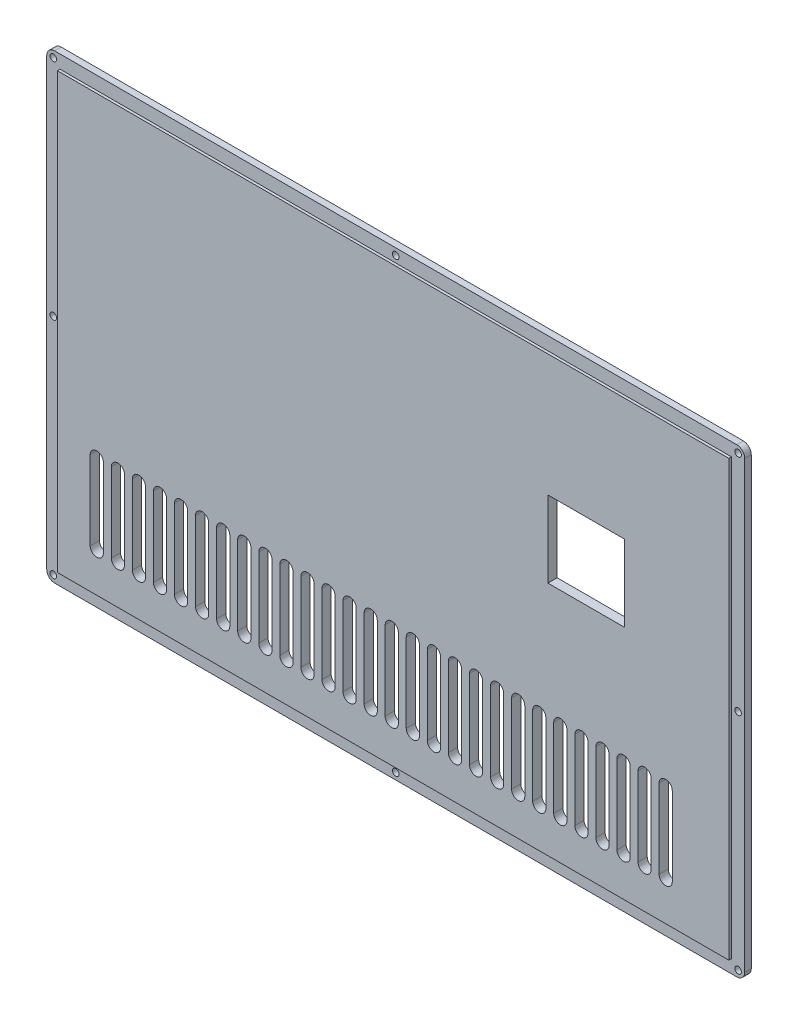
SolidWorks part; units mm, degrees
ref_plane "Front Plane" through (0, 0, 0) normal (0, 0, 1) x (1, 0, 0)
ref_plane "Top Plane" through (0, 0, 0) normal (0, 1, 0) x (1, 0, 0)
ref_plane "Right Plane" through (0, 0, 0) normal (1, 0, 0) x (0, 0, -1)
sketch "Sketch1" plane through (0, 0, 0) normal (0, 0, 1) x (1, 0, 0)
  line L1 (-132.5, 87.5) -> (132.5, 87.5)
  line L2 (-132.5, 87.5) -> (-132.5, -87.5)
  line L3 (-132.5, -87.5) -> (132.5, -87.5)
  line L4 (132.5, 87.5) -> (132.5, -87.5)
  point P4 (-132.5, 0)
  point P6 (0, 87.5)
  dimension "D1" = 265
  dimension "D2" = 175
extrude "Boss-Extrude1" add sketch "Sketch1" along normal blind 2.5
sketch "Sketch2" plane through (0, 0, 2.5) normal (0, 0, 1) x (1, 0, 0)
  line L0 (132.5, 87.5) -> (-132.5, 87.5) construction
  line L1 (-127.5, 82.5) -> (127.5, 82.5)
  line L2 (-127.5, 82.5) -> (-127.5, -82.5)
  line L3 (-127.5, -82.5) -> (127.5, -82.5)
  line L4 (127.5, 82.5) -> (127.5, -82.5)
  line L5 (-132.5, 87.5) -> (-132.5, -87.5) construction
  point P4 (-127.5, 0)
  point P6 (0, 82.5)
  dimension "D1" = 5
  dimension "D2" = 5
extrude "Boss-Extrude2" add sketch "Sketch2" along normal blind 1
sketch "Sketch3" plane through (0, 0, 0) normal (0, 0, -1) x (-1, 0, 0)
  line L0 (132.5, -87.5) -> (-132.5, -87.5) construction
  line L1 (132.5, 87.5) -> (132.5, -87.5) construction
  line L2 (110, -67.5) -> (110, -37.5)
  line L3 (115, -67.5) -> (115, -37.5)
  arc A0 (110, -67.5) -> (115, -67.5) centre (112.5, -67.5) ccw
  arc A1 (115, -37.5) -> (110, -37.5) centre (112.5, -37.5) ccw
  point P11 (112.5, -35)
  point P15 (112.5, -70)
  dimension "D1" = 5
  dimension "D2" = 20
  dimension "D3" = 20
  dimension "D4" = 30
extrude "Cut-Extrude1" cut sketch "Sketch3" against normal through all
pattern_linear "LPattern1" count 28 spacing 8 along (1, 0, 0) of "Cut-Extrude1"
mirror "Mirror2" [suppressed] about plane through (0, 0, 0) normal (0, 1, 0)
fillet "Fillet3" radius 3 4 edges at (132.5, -87.5, 1.25) (132.5, 87.5, 1.25) (-132.5, 87.5, 1.25) (-132.5, -87.5, 1.25)
sketch "Sketch5" plane through (0, 0, 0) normal (0, 0, -1) x (-1, 0, 0)
  line L1 (-58.78, 7.14) -> (-87.78, 7.14)
  line L2 (-58.78, 7.14) -> (-58.78, 36.14)
  line L3 (-58.78, 36.14) -> (-87.78, 36.14)
  line L4 (-87.78, 7.14) -> (-87.78, 36.14)
  line L5 (-132.5, -84.5) -> (-132.5, 84.5) construction
  point P4 (-58.78, 21.64)
  point P5 (-73.28, 7.14)
  dimension "D1" = 29
  dimension "D2" = 29
  dimension "D3" = 21.64
  dimension "D4" = 59.22
extrude "Cut-Extrude3" cut sketch "Sketch5" against normal through all
sketch "Sketch7" plane through (0, 0, 0) normal (0, 0, -1) x (-1, 0, 0)
  line L0 (-129.5, 87.5) -> (129.5, 87.5) construction
  line L1 (130, 85) -> (-130, 85) construction
  line L2 (130, 85) -> (130, -85) construction
  line L3 (130, -85) -> (-130, -85) construction
  line L4 (-130, 85) -> (-130, -85) construction
  line L5 (129.5, -87.5) -> (-129.5, -87.5) construction
  line L6 (132.5, 84.5) -> (132.5, -84.5) construction
  line L7 (-132.5, -84.5) -> (-132.5, 84.5) construction
  circle A0 centre (130, -85) radius 1.25
  circle A1 centre (130, 0) radius 1.25
  circle A2 centre (130, 85) radius 1.25
  circle A3 centre (0, 85) radius 1.25
  circle A4 centre (-130, 85) radius 1.25
  circle A5 centre (-130, 0) radius 1.25
  circle A6 centre (-130, -85) radius 1.25
  circle A7 centre (0, -85) radius 1.25
  dimension "D5" = 2.5
  dimension "D1" = 2.5
  dimension "D2" = 2.5
  dimension "D3" = 2.5
  dimension "D4" = 2.5
extrude "Cut-Extrude4" cut sketch "Sketch7" against normal through all
sketch "Sketch8" plane through (0, 0, 0) normal (0, 0, -1) x (-1, 0, 0)
  line L0 (69.0973, 92.1728) -> (202.4306, 92.1728) construction
  line L1 (85.3423, 47.1146) -> (-9.836, 47.1146)
  line L2 (-33.6608, 23.2899) -> (-33.6608, 20.6474)
  line L3 (-9.836, -3.1774) -> (85.3423, -3.1774)
  line L4 (109.167, 20.6474) -> (109.167, 23.2899)
  line L5 (9.765, 10.2781) -> (10.9597, 11.2255)
  line L6 (24.4102, 24.4248) -> (22.062, 24.4248)
  line L7 (32.0726, 29.8453) -> (30.8984, 28.8759)
  line L8 (22.062, 26.0112) -> (24.4102, 26.0112)
  line L9 (24.4102, 21.2516) -> (22.062, 21.2516)
  line L10 (34.4002, 31.8285) -> (33.2466, 30.837)
  line L11 (22.062, 22.8382) -> (24.3277, 22.8382)
  line L12 (12.0719, 12.2611) -> (13.2254, 13.2529)
  line L13 (22.062, 19.665) -> (24.3277, 19.665)
  line L14 (14.3995, 14.2446) -> (15.5736, 15.2139)
  line L15 (24.4102, 18.0785) -> (22.062, 18.0785)
  line L16 (36.7071, 33.8117) -> (35.5125, 32.8641)
  line L17 (62.0839, 16.6943) -> (63.2168, 15.7467)
  line L18 (63.2373, 28.7028) -> (62.0632, 27.7966)
  line L19 (64.4114, 14.8404) -> (65.5237, 13.8723)
  line L20 (65.5649, 30.5566) -> (64.4114, 29.6298)
  line L21 (66.6773, 12.9454) -> (67.8514, 12.0389)
  line L22 (67.8719, 32.4105) -> (66.6773, 31.5247)
  line L23 (93.1662, 16.6943) -> (94.299, 15.7467)
  line L24 (94.3196, 28.7028) -> (93.1455, 27.7966)
  line L25 (95.4936, 14.8404) -> (96.606, 13.8723)
  line L26 (96.6472, 30.5566) -> (95.4936, 29.6298)
  line L27 (97.7595, 12.9454) -> (98.9336, 12.0389)
  line L28 (98.9542, 32.4105) -> (97.7595, 31.5247)
  line L29 (132.5, 0) -> (-55.3342, 0) construction
  line L30 (132.5, 84.5) -> (132.5, -84.5) construction
  spline S0 degree 3 poles (2.0716, 26.8386) (1.4466, 28.3012) (0.6021, 29.5644) (-0.4619, 30.6288) knots 15 15 15 15 16 16 16 16
  spline S1 degree 3 poles (2.0716, 17.6314) (2.6963, 19.0939) (3.0088, 20.6285) (3.0088, 22.2352) (3.0088, 23.8418) (2.6963, 25.3762) (2.0716, 26.8386) knots 13 13 13 13 14 14 14 15 15 15 15
  spline S2 degree 3 poles (-0.4619, 13.8415) (0.6021, 14.9055) (1.4466, 16.169) (2.0716, 17.6314) knots 12 12 12 12 13 13 13 13
  spline S3 degree 3 poles (-4.252, 11.3078) (-2.7895, 11.9325) (-1.5263, 12.777) (-0.4619, 13.8415) knots 11 11 11 11 12 12 12 12
  spline S4 degree 3 poles (-13.4592, 11.3078) (-11.9968, 10.6829) (-10.4622, 10.3707) (-8.8556, 10.3707) (-7.249, 10.3707) (-5.7145, 10.6829) (-4.252, 11.3078) knots 9 9 9 9 10 10 10 11 11 11 11
  spline S5 degree 3 poles (-17.2493, 13.8415) (-16.1853, 12.777) (-14.9217, 11.9325) (-13.4592, 11.3078) knots 8 8 8 8 9 9 9 9
  spline S6 degree 3 poles (-19.7829, 17.6314) (-19.1581, 16.169) (-18.3137, 14.9055) (-17.2493, 13.8415) knots 7 7 7 7 8 8 8 8
  spline S7 degree 3 poles (-19.7829, 26.8386) (-20.4079, 25.3762) (-20.7201, 23.8418) (-20.7201, 22.2352) (-20.7201, 20.6285) (-20.4079, 19.0939) (-19.7829, 17.6314) knots 5 5 5 5 6 6 6 7 7 7 7
  spline S8 degree 3 poles (-17.2493, 30.6288) (-18.3137, 29.5644) (-19.1581, 28.3012) (-19.7829, 26.8386) knots 4 4 4 4 5 5 5 5
  spline S9 degree 3 poles (-13.4592, 33.1623) (-14.9217, 32.5372) (-16.1853, 31.6928) (-17.2493, 30.6288) knots 3 3 3 3 4 4 4 4
  spline S10 degree 3 poles (-4.252, 33.1623) (-5.7145, 33.7871) (-7.249, 34.0996) (-8.8556, 34.0996) (-10.4622, 34.0996) (-11.9968, 33.7871) (-13.4592, 33.1623) knots 1 1 1 1 2 2 2 3 3 3 3
  spline S11 degree 3 poles (-0.4619, 30.6288) (-1.5263, 31.6928) (-2.7895, 32.5372) (-4.252, 33.1623) knots 0 0 0 0 1 1 1 1
  spline S12 degree 3 poles (0.1354, 27.4464) (1.0623, 25.8531) (1.5257, 24.1164) (1.5257, 22.2352) (1.5257, 20.3536) (1.0623, 18.6165) (0.1354, 17.0238) knots 10 10 10 10 11 11 11 12 12 12 12
  spline S13 degree 3 poles (-3.6443, 31.226) (-2.0515, 30.2993) (-0.7915, 29.0393) (0.1354, 27.4464) knots 9 9 9 9 10 10 10 10
  spline S14 degree 3 poles (-14.0669, 31.226) (-12.4741, 32.153) (-10.7372, 32.6165) (-8.8556, 32.6165) (-6.9744, 32.6165) (-5.2375, 32.153) (-3.6443, 31.226) knots 7 7 7 7 8 8 8 9 9 9 9
  spline S15 degree 3 poles (-17.8467, 27.4464) (-16.9197, 29.0393) (-15.6601, 30.2993) (-14.0669, 31.226) knots 6 6 6 6 7 7 7 7
  spline S16 degree 3 poles (-17.8467, 17.0238) (-18.7735, 18.6165) (-19.237, 20.3536) (-19.237, 22.2352) (-19.237, 24.1164) (-18.7735, 25.8531) (-17.8467, 27.4464) knots 4 4 4 4 5 5 5 6 6 6 6
  spline S17 degree 3 poles (-14.0669, 13.244) (-15.6601, 14.171) (-16.9197, 15.4307) (-17.8467, 17.0238) knots 3 3 3 3 4 4 4 4
  spline S18 degree 3 poles (-3.6443, 13.244) (-5.2375, 12.3172) (-6.9744, 11.8536) (-8.8556, 11.8536) (-10.7372, 11.8536) (-12.4741, 12.3172) (-14.0669, 13.244) knots 1 1 1 1 2 2 2 3 3 3 3
  spline S19 degree 3 poles (0.1354, 17.0238) (-0.7915, 15.4307) (-2.0515, 14.171) (-3.6443, 13.244) knots 0 0 0 0 1 1 1 1
  spline S20 degree 3 poles (-2.563, 28.5175) (-4.3003, 30.2612) (-6.3977, 31.1334) (-8.8556, 31.1334) knots 7 7 7 7 8 8 8 8
  spline S21 degree 3 poles (-2.563, 15.9527) (-0.8259, 17.6964) (0.0427, 19.7906) (0.0427, 22.2352) (0.0427, 24.6791) (-0.8259, 26.7734) (-2.563, 28.5175) knots 5 5 5 5 6 6 6 7 7 7 7
  spline S22 degree 3 poles (-15.1483, 15.9527) (-13.4113, 14.2086) (-11.3138, 13.3367) (-8.8556, 13.3367) (-6.3977, 13.3367) (-4.3003, 14.2086) (-2.563, 15.9527) knots 3 3 3 3 4 4 4 5 5 5 5
  spline S23 degree 3 poles (-15.1483, 28.5175) (-16.8857, 26.7734) (-17.754, 24.6791) (-17.754, 22.2352) (-17.754, 19.7906) (-16.8857, 17.6964) (-15.1483, 15.9527) knots 1 1 1 1 2 2 2 3 3 3 3
  spline S24 degree 3 poles (-8.8556, 31.1334) (-11.3138, 31.1334) (-13.4113, 30.2612) (-15.1483, 28.5175) knots 0 0 0 0 1 1 1 1
  spline S25 degree 3 poles (4.8009, 27.9922) (4.0181, 29.8254) (2.964, 31.4045) (1.639, 32.7298) knots 15 15 15 15 16 16 16 16
  spline S26 degree 3 poles (4.8009, 16.478) (5.5836, 18.3112) (5.9749, 20.2301) (5.9749, 22.2352) (5.9749, 24.2399) (5.5836, 26.159) (4.8009, 27.9922) knots 13 13 13 13 14 14 14 15 15 15 15
  spline S27 degree 3 poles (1.639, 11.7404) (2.964, 13.0655) (4.0181, 14.6446) (4.8009, 16.478) knots 12 12 12 12 13 13 13 13
  spline S28 degree 3 poles (-3.0985, 8.5786) (-1.2652, 9.3612) (0.3137, 10.4151) (1.639, 11.7404) knots 11 11 11 11 12 12 12 12
  spline S29 degree 3 poles (-14.6128, 8.5786) (-12.7795, 7.796) (-10.8607, 7.4045) (-8.8556, 7.4045) (-6.8509, 7.4045) (-4.9317, 7.796) (-3.0985, 8.5786) knots 9 9 9 9 10 10 10 11 11 11 11
  spline S30 degree 3 poles (-19.3503, 11.7404) (-18.0253, 10.4151) (-16.446, 9.3612) (-14.6128, 8.5786) knots 8 8 8 8 9 9 9 9
  spline S31 degree 3 poles (-22.5121, 16.478) (-21.7294, 14.6446) (-20.6757, 13.0655) (-19.3503, 11.7404) knots 7 7 7 7 8 8 8 8
  spline S32 degree 3 poles (-22.5121, 27.9922) (-23.2948, 26.159) (-23.6862, 24.2399) (-23.6862, 22.2352) (-23.6862, 20.2301) (-23.2948, 18.3112) (-22.5121, 16.478) knots 5 5 5 5 6 6 6 7 7 7 7
  spline S33 degree 3 poles (-19.3503, 32.7298) (-20.6757, 31.4045) (-21.7294, 29.8254) (-22.5121, 27.9922) knots 4 4 4 4 5 5 5 5
  spline S34 degree 3 poles (-14.6128, 35.8915) (-16.446, 35.1088) (-18.0253, 34.0547) (-19.3503, 32.7298) knots 3 3 3 3 4 4 4 4
  spline S35 degree 3 poles (-3.0985, 35.8915) (-4.9317, 36.6743) (-6.8509, 37.0656) (-8.8556, 37.0656) (-10.8607, 37.0656) (-12.7795, 36.6743) (-14.6128, 35.8915) knots 1 1 1 1 2 2 2 3 3 3 3
  spline S36 degree 3 poles (1.639, 32.7298) (0.3137, 34.0547) (-1.2652, 35.1088) (-3.0985, 35.8915) knots 0 0 0 0 1 1 1 1
  spline S37 degree 3 poles (3.4311, 27.4257) (4.1381, 25.778) (4.4919, 24.0478) (4.4919, 22.2352) (4.4919, 20.4225) (4.1381, 18.6922) (3.4311, 17.0443) knots 14 14 14 14 15 15 15 16 16 16 16
  spline S38 degree 3 poles (0.5885, 31.6792) (1.7762, 30.4914) (2.7237, 29.0737) (3.4311, 27.4257) knots 13 13 13 13 14 14 14 14
  spline S39 degree 3 poles (-3.6649, 34.5217) (-2.0171, 33.8143) (-0.5994, 32.8669) (0.5885, 31.6792) knots 12 12 12 12 13 13 13 13
  spline S40 degree 3 poles (-14.0463, 34.5217) (-12.3985, 35.2288) (-10.6682, 35.5825) (-8.8556, 35.5825) (-7.043, 35.5825) (-5.3128, 35.2288) (-3.6649, 34.5217) knots 10 10 10 10 11 11 11 12 12 12 12
  spline S41 degree 3 poles (-18.2998, 31.6792) (-17.1122, 32.8669) (-15.6942, 33.8143) (-14.0463, 34.5217) knots 9 9 9 9 10 10 10 10
  spline S42 degree 3 poles (-21.1423, 27.4257) (-20.4352, 29.0737) (-19.4878, 30.4914) (-18.2998, 31.6792) knots 8 8 8 8 9 9 9 9
  spline S43 degree 3 poles (-21.1423, 17.0443) (-21.8498, 18.6922) (-22.2031, 20.4225) (-22.2031, 22.2352) (-22.2031, 24.0478) (-21.8498, 25.778) (-21.1423, 27.4257) knots 6 6 6 6 7 7 7 8 8 8 8
  spline S44 degree 3 poles (-18.2998, 12.7909) (-19.4878, 13.9786) (-20.4352, 15.3966) (-21.1423, 17.0443) knots 5 5 5 5 6 6 6 6
  spline S45 degree 3 poles (-14.0463, 9.9483) (-15.6942, 10.6554) (-17.1122, 11.6029) (-18.2998, 12.7909) knots 4 4 4 4 5 5 5 5
  spline S46 degree 3 poles (-3.6649, 9.9483) (-5.3128, 9.241) (-7.043, 8.8876) (-8.8556, 8.8876) (-10.6682, 8.8876) (-12.3985, 9.241) (-14.0463, 9.9483) knots 2 2 2 2 3 3 3 4 4 4 4
  spline S47 degree 3 poles (0.5885, 12.7909) (-0.5994, 11.6029) (-2.0171, 10.6554) (-3.6649, 9.9483) knots 1 1 1 1 2 2 2 2
  spline S48 degree 3 poles (3.4311, 17.0443) (2.7237, 15.3966) (1.7762, 13.9786) (0.5885, 12.7909) knots 0 0 0 0 1 1 1 1
  spline S49 degree 3 poles (-9.836, 47.1146) (-22.9941, 47.1146) (-33.6608, 36.4479) (-33.6608, 23.2899) knots 1 1 1 1 2 2 2 2
  spline S50 degree 3 poles (-33.6608, 20.6474) (-33.6608, 7.4893) (-22.9941, -3.1774) (-9.836, -3.1774) knots 3 3 3 3 4 4 4 4
  spline S51 degree 3 poles (85.3423, -3.1774) (98.5003, -3.1774) (109.167, 7.4893) (109.167, 20.6474) knots 5 5 5 5 6 6 6 6
  spline S52 degree 3 poles (109.167, 23.2899) (109.167, 36.4479) (98.5003, 47.1146) (85.3423, 47.1146) knots 7 7 7 7 8 8 8 8
  spline S53 degree 3 poles (6.1603, 28.569) (7.0254, 26.5571) (7.458, 24.4459) (7.458, 22.2352) (7.458, 20.0241) (7.0254, 17.9127) (6.1603, 15.9012) knots 14 14 14 14 15 15 15 16 16 16 16
  spline S54 degree 3 poles (2.6792, 33.7701) (4.1346, 32.3143) (5.2952, 30.5805) (6.1603, 28.569) knots 13 13 13 13 14 14 14 14
  spline S55 degree 3 poles (-2.5217, 37.2509) (-0.5102, 36.3859) (1.2235, 35.2253) (2.6792, 33.7701) knots 12 12 12 12 13 13 13 13
  spline S56 degree 3 poles (-15.1895, 37.2509) (-13.178, 38.116) (-11.0667, 38.5486) (-8.8556, 38.5486) (-6.6449, 38.5486) (-4.5336, 38.116) (-2.5217, 37.2509) knots 10 10 10 10 11 11 11 12 12 12 12
  spline S57 degree 3 poles (-20.3905, 33.7701) (-18.9351, 35.2253) (-17.2014, 36.3859) (-15.1895, 37.2509) knots 9 9 9 9 10 10 10 10
  spline S58 degree 3 poles (-23.8715, 28.569) (-23.0065, 30.5805) (-21.8462, 32.3143) (-20.3905, 33.7701) knots 8 8 8 8 9 9 9 9
  spline S59 degree 3 poles (-23.8715, 15.9012) (-24.7366, 17.9127) (-25.1693, 20.0241) (-25.1693, 22.2352) (-25.1693, 24.4459) (-24.7366, 26.5571) (-23.8715, 28.569) knots 6 6 6 6 7 7 7 8 8 8 8
  spline S60 degree 3 poles (-20.3905, 10.7003) (-21.8462, 12.1555) (-23.0065, 13.8893) (-23.8715, 15.9012) knots 5 5 5 5 6 6 6 6
  spline S61 degree 3 poles (-15.1895, 7.2191) (-17.2014, 8.0841) (-18.9351, 9.2445) (-20.3905, 10.7003) knots 4 4 4 4 5 5 5 5
  spline S62 degree 3 poles (-2.5217, 7.2191) (-4.5336, 6.354) (-6.6449, 5.9214) (-8.8556, 5.9214) (-11.0667, 5.9214) (-13.178, 6.354) (-15.1895, 7.2191) knots 2 2 2 2 3 3 3 4 4 4 4
  spline S63 degree 3 poles (2.6792, 10.7003) (1.2235, 9.2445) (-0.5102, 8.0841) (-2.5217, 7.2191) knots 1 1 1 1 2 2 2 2
  spline S64 degree 3 poles (6.1603, 15.9012) (5.2952, 13.8893) (4.1346, 12.1555) (2.6792, 10.7003) knots 0 0 0 0 1 1 1 1
  spline S65 degree 3 poles (35.4713, 11.7545) (34.8808, 10.5058) (34.0325, 9.4078) (32.9274, 8.4604) knots 0 0 0 0 1 1 1 1
  spline S66 degree 3 poles (32.9274, 8.4604) (31.8218, 7.5126) (30.4109, 6.7636) (28.6945, 6.2127) knots 1 1 1 1 2 2 2 2
  spline S67 degree 3 poles (28.6945, 6.2127) (26.9778, 5.6617) (25.0692, 5.3862) (22.9683, 5.3862) knots 2 2 2 2 3 3 3 3
  spline S68 degree 3 poles (22.9683, 5.3862) (20.3179, 5.3862) (17.8394, 5.816) (15.5324, 6.6754) knots 3 3 3 3 4 4 4 4
  spline S69 degree 3 poles (15.5324, 6.6754) (13.2254, 7.5347) (11.3027, 8.7357) (9.765, 10.2781) knots 4 4 4 4 5 5 5 5
  spline S70 degree 3 poles (10.9597, 11.2255) (12.3603, 9.8738) (14.1112, 8.8272) (16.2121, 8.0855) knots 6 6 6 6 7 7 7 7
  spline S71 degree 3 poles (16.2121, 8.0855) (18.3132, 7.3436) (20.565, 6.9728) (22.9683, 6.9728) knots 7 7 7 7 8 8 8 8
  spline S72 degree 3 poles (22.9683, 6.9728) (26.6759, 6.9728) (29.5871, 7.8102) (31.7018, 9.4848) knots 8 8 8 8 9 9 9 9
  spline S73 degree 3 poles (31.7018, 9.4848) (33.8163, 11.1596) (34.874, 13.2529) (34.874, 15.7649) knots 9 9 9 9 10 10 10 10
  spline S74 degree 3 poles (34.874, 15.7649) (34.874, 18.4236) (33.9677, 20.5317) (32.155, 22.0888) knots 10 10 10 10 11 11 11 11
  spline S75 degree 3 poles (32.155, 22.0888) (30.3424, 23.646) (27.7605, 24.4248) (24.4102, 24.4248) knots 11 11 11 11 12 12 12 12
  spline S76 degree 3 poles (22.062, 24.4248) (18.0521, 24.4248) (16.0474, 25.7247) (16.0474, 28.325) knots 13 13 13 13 14 14 14 14
  spline S77 degree 3 poles (16.0474, 28.325) (16.0474, 29.5) (16.6685, 30.4658) (17.9115, 31.2226) knots 14 14 14 14 15 15 15 15
  spline S78 degree 3 poles (17.9115, 31.2226) (19.1542, 31.9791) (21.0182, 32.3573) (23.5038, 32.3573) knots 15 15 15 15 16 16 16 16
  spline S79 degree 3 poles (23.5038, 32.3573) (25.2476, 32.3573) (26.8681, 32.1404) (28.365, 31.7073) knots 16 16 16 16 17 17 17 17
  spline S80 degree 3 poles (28.365, 31.7073) (29.8615, 31.2738) (31.0973, 30.6531) (32.0726, 29.8453) knots 17 17 17 17 18 18 18 18
  spline S81 degree 3 poles (30.8984, 28.8759) (29.1819, 30.139) (26.7171, 30.7707) (23.5038, 30.7707) knots 19 19 19 19 20 20 20 20
  spline S82 degree 3 poles (23.5038, 30.7707) (21.444, 30.7707) (19.9333, 30.5429) (18.9723, 30.0876) knots 20 20 20 20 21 21 21 21
  spline S83 degree 3 poles (18.9723, 30.0876) (18.0109, 29.6323) (17.5304, 29.0445) (17.5304, 28.325) knots 21 21 21 21 22 22 22 22
  spline S84 degree 3 poles (17.5304, 28.325) (17.5304, 27.4876) (17.8667, 26.8925) (18.5397, 26.54) knots 22 22 22 22 23 23 23 23
  spline S85 degree 3 poles (18.5397, 26.54) (19.2124, 26.1874) (20.3865, 26.0112) (22.062, 26.0112) knots 23 23 23 23 24 24 24 24
  spline S86 degree 3 poles (24.4102, 26.0112) (28.2275, 26.0112) (31.173, 25.0818) (33.2466, 23.2239) knots 25 25 25 25 26 26 26 26
  spline S87 degree 3 poles (33.2466, 23.2239) (35.3199, 21.3652) (36.3569, 18.879) (36.3569, 15.7649) knots 26 26 26 26 27 27 27 27
  spline S88 degree 3 poles (36.3569, 15.7649) (36.3569, 14.3399) (36.0615, 13.0029) (35.4713, 11.7545) knots 27 27 27 27 28 28 28 28
  spline S89 degree 3 poles (30.0231, 19.8303) (28.7666, 20.7777) (26.8955, 21.2516) (24.4102, 21.2516) knots 0 0 0 0 1 1 1 1
  spline S90 degree 3 poles (22.062, 21.2516) (19.1783, 21.2516) (16.9605, 21.8796) (15.4088, 23.1356) knots 2 2 2 2 3 3 3 3
  spline S91 degree 3 poles (15.4088, 23.1356) (13.8569, 24.3917) (13.0813, 26.1214) (13.0813, 28.325) knots 3 3 3 3 4 4 4 4
  spline S92 degree 3 poles (13.0813, 28.325) (13.0813, 30.3813) (13.9944, 32.0963) (15.8207, 33.47) knots 4 4 4 4 5 5 5 5
  spline S93 degree 3 poles (15.8207, 33.47) (17.647, 34.8436) (20.2082, 35.5304) (23.5038, 35.5304) knots 5 5 5 5 6 6 6 6
  spline S94 degree 3 poles (23.5038, 35.5304) (25.7008, 35.5304) (27.7503, 35.2071) (29.6523, 34.5607) knots 6 6 6 6 7 7 7 7
  spline S95 degree 3 poles (29.6523, 34.5607) (31.5541, 33.9143) (33.1367, 33.0035) (34.4002, 31.8285) knots 7 7 7 7 8 8 8 8
  spline S96 degree 3 poles (33.2466, 30.837) (32.1206, 31.8209) (30.706, 32.5849) (29.0035, 33.1286) knots 9 9 9 9 10 10 10 10
  spline S97 degree 3 poles (29.0035, 33.1286) (27.3007, 33.6717) (25.4673, 33.9439) (23.5038, 33.9439) knots 10 10 10 10 11 11 11 11
  spline S98 degree 3 poles (23.5038, 33.9439) (20.6063, 33.9439) (18.392, 33.4149) (16.8609, 32.3573) knots 11 11 11 11 12 12 12 12
  spline S99 degree 3 poles (16.8609, 32.3573) (15.3296, 31.2997) (14.5643, 29.9555) (14.5643, 28.325) knots 12 12 12 12 13 13 13 13
  spline S100 degree 3 poles (14.5643, 28.325) (14.5643, 26.5621) (15.1926, 25.2069) (16.449, 24.2595) knots 13 13 13 13 14 14 14 14
  spline S101 degree 3 poles (16.449, 24.2595) (17.7055, 23.3119) (19.5763, 22.8382) (22.062, 22.8382) knots 14 14 14 14 15 15 15 15
  spline S102 degree 3 poles (24.3277, 22.8382) (27.2526, 22.8382) (29.4944, 22.2102) (31.053, 20.9542) knots 16 16 16 16 17 17 17 17
  spline S103 degree 3 poles (31.053, 20.9542) (32.6114, 19.6982) (33.3909, 17.9683) (33.3909, 15.7649) knots 17 17 17 17 18 18 18 18
  spline S104 degree 3 poles (33.3909, 15.7649) (33.3909, 13.7081) (32.4774, 11.9931) (30.6514, 10.6197) knots 18 18 18 18 19 19 19 19
  spline S105 degree 3 poles (30.6514, 10.6197) (28.8248, 9.2458) (26.264, 8.5594) (22.9683, 8.5594) knots 19 19 19 19 20 20 20 20
  spline S106 degree 3 poles (22.9683, 8.5594) (20.7711, 8.5594) (18.7215, 8.8823) (16.8198, 9.5289) knots 20 20 20 20 21 21 21 21
  spline S107 degree 3 poles (16.8198, 9.5289) (14.9177, 10.1752) (13.3352, 11.0859) (12.0719, 12.2611) knots 21 21 21 21 22 22 22 22
  spline S108 degree 3 poles (13.2254, 13.2529) (14.3512, 12.2686) (15.7658, 11.5045) (17.4686, 10.9612) knots 23 23 23 23 24 24 24 24
  spline S109 degree 3 poles (17.4686, 10.9612) (19.1712, 10.4175) (21.0044, 10.146) (22.9683, 10.146) knots 24 24 24 24 25 25 25 25
  spline S110 degree 3 poles (22.9683, 10.146) (25.8656, 10.146) (28.0798, 10.6748) (29.6111, 11.7325) knots 25 25 25 25 26 26 26 26
  spline S111 degree 3 poles (29.6111, 11.7325) (31.1422, 12.7901) (31.9078, 14.1344) (31.9078, 15.7649) knots 26 26 26 26 27 27 27 27
  spline S112 degree 3 poles (31.9078, 15.7649) (31.9078, 17.5277) (31.2795, 18.8829) (30.0231, 19.8303) knots 27 27 27 27 28 28 28 28
  spline S113 degree 3 poles (35.5125, 32.8641) (34.1117, 34.2156) (32.361, 35.262) (30.2599, 36.0041) knots 0 0 0 0 1 1 1 1
  spline S114 degree 3 poles (30.2599, 36.0041) (28.159, 36.7459) (25.9067, 37.117) (23.5038, 37.117) knots 1 1 1 1 2 2 2 2
  spline S115 degree 3 poles (23.5038, 37.117) (19.7962, 37.117) (16.8848, 36.2796) (14.7703, 34.605) knots 2 2 2 2 3 3 3 3
  spline S116 degree 3 poles (14.7703, 34.605) (12.6555, 32.9302) (11.5982, 30.837) (11.5982, 28.325) knots 3 3 3 3 4 4 4 4
  spline S117 degree 3 poles (11.5982, 28.325) (11.5982, 25.6659) (12.5045, 23.5578) (14.3171, 22.0008) knots 4 4 4 4 5 5 5 5
  spline S118 degree 3 poles (14.3171, 22.0008) (16.1297, 20.4434) (18.7113, 19.665) (22.062, 19.665) knots 5 5 5 5 6 6 6 6
  spline S119 degree 3 poles (24.3277, 19.665) (28.3923, 19.665) (30.4247, 18.3651) (30.4247, 15.7649) knots 7 7 7 7 8 8 8 8
  spline S120 degree 3 poles (30.4247, 15.7649) (30.4247, 14.5895) (29.8034, 13.6236) (28.5607, 12.8672) knots 8 8 8 8 9 9 9 9
  spline S121 degree 3 poles (28.5607, 12.8672) (27.3177, 12.1104) (25.4536, 11.7325) (22.9683, 11.7325) knots 9 9 9 9 10 10 10 10
  spline S122 degree 3 poles (22.9683, 11.7325) (21.2242, 11.7325) (19.6037, 11.949) (18.1072, 12.3825) knots 10 10 10 10 11 11 11 11
  spline S123 degree 3 poles (18.1072, 12.3825) (16.6102, 12.8156) (15.3744, 13.4364) (14.3995, 14.2446) knots 11 11 11 11 12 12 12 12
  spline S124 degree 3 poles (15.5736, 15.2139) (17.29, 13.9505) (19.755, 13.3189) (22.9683, 13.3189) knots 13 13 13 13 14 14 14 14
  spline S125 degree 3 poles (22.9683, 13.3189) (25.0282, 13.3189) (26.5384, 13.5466) (27.4999, 14.002) knots 14 14 14 14 15 15 15 15
  spline S126 degree 3 poles (27.4999, 14.002) (28.4608, 14.4571) (28.9418, 15.0449) (28.9418, 15.7649) knots 15 15 15 15 16 16 16 16
  spline S127 degree 3 poles (28.9418, 15.7649) (28.9418, 16.6021) (28.6051, 17.1971) (27.9324, 17.5497) knots 16 16 16 16 17 17 17 17
  spline S128 degree 3 poles (27.9324, 17.5497) (27.2595, 17.9024) (26.0853, 18.0785) (24.4102, 18.0785) knots 17 17 17 17 18 18 18 18
  spline S129 degree 3 poles (22.062, 18.0785) (18.2443, 18.0785) (15.2988, 19.0075) (13.2254, 20.866) knots 19 19 19 19 20 20 20 20
  spline S130 degree 3 poles (13.2254, 20.866) (11.1518, 22.7243) (10.1152, 25.2103) (10.1152, 28.325) knots 20 20 20 20 21 21 21 21
  spline S131 degree 3 poles (10.1152, 28.325) (10.1152, 29.7496) (10.4102, 31.0864) (11.0009, 32.3353) knots 21 21 21 21 22 22 22 22
  spline S132 degree 3 poles (11.0009, 32.3353) (11.5911, 33.5837) (12.4391, 34.6821) (13.5447, 35.6295) knots 22 22 22 22 23 23 23 23
  spline S133 degree 3 poles (13.5447, 35.6295) (14.65, 36.5771) (16.0609, 37.3262) (17.7776, 37.8772) knots 23 23 23 23 24 24 24 24
  spline S134 degree 3 poles (17.7776, 37.8772) (19.494, 38.4281) (21.4028, 38.7034) (23.5038, 38.7034) knots 24 24 24 24 25 25 25 25
  spline S135 degree 3 poles (23.5038, 38.7034) (26.1539, 38.7034) (28.6328, 38.2736) (30.9397, 37.4145) knots 25 25 25 25 26 26 26 26
  spline S136 degree 3 poles (30.9397, 37.4145) (33.2466, 36.5549) (35.1691, 35.354) (36.7071, 33.8117) knots 26 26 26 26 27 27 27 27
  spline S137 degree 3 poles (48.8291, 15.9527) (50.566, 14.2086) (52.6635, 13.3367) (55.1217, 13.3367) knots 0 0 0 0 1 1 1 1
  spline S138 degree 3 poles (55.1217, 13.3367) (56.4948, 13.3367) (57.7924, 13.6355) (59.0147, 14.2326) knots 1 1 1 1 2 2 2 2
  spline S139 degree 3 poles (59.0147, 14.2326) (60.2368, 14.8301) (61.2599, 15.6505) (62.0839, 16.6943) knots 2 2 2 2 3 3 3 3
  spline S140 degree 3 poles (63.2168, 15.7467) (62.2555, 14.5382) (61.0675, 13.5871) (59.6532, 12.8939) knots 4 4 4 4 5 5 5 5
  spline S141 degree 3 poles (59.6532, 12.8939) (58.2387, 12.2004) (56.7283, 11.8536) (55.1217, 11.8536) knots 5 5 5 5 6 6 6 6
  spline S142 degree 3 poles (55.1217, 11.8536) (53.2403, 11.8536) (51.5032, 12.3172) (49.9105, 13.244) knots 6 6 6 6 7 7 7 7
  spline S143 degree 3 poles (49.9105, 13.244) (48.3174, 14.171) (47.0577, 15.4307) (46.1307, 17.0238) knots 7 7 7 7 8 8 8 8
  spline S144 degree 3 poles (46.1307, 17.0238) (45.2038, 18.6165) (44.7403, 20.3536) (44.7403, 22.2352) knots 8 8 8 8 9 9 9 9
  spline S145 degree 3 poles (44.7403, 22.2352) (44.7403, 24.1164) (45.2038, 25.8531) (46.1307, 27.4464) knots 9 9 9 9 10 10 10 10
  spline S146 degree 3 poles (46.1307, 27.4464) (47.0577, 29.0393) (48.3174, 30.2993) (49.9105, 31.226) knots 10 10 10 10 11 11 11 11
  spline S147 degree 3 poles (49.9105, 31.226) (51.5032, 32.153) (53.2403, 32.6165) (55.1217, 32.6165) knots 11 11 11 11 12 12 12 12
  spline S148 degree 3 poles (55.1217, 32.6165) (56.7283, 32.6165) (58.2424, 32.2696) (59.6635, 31.5762) knots 12 12 12 12 13 13 13 13
  spline S149 degree 3 poles (59.6635, 31.5762) (61.0848, 30.8827) (62.276, 29.9249) (63.2373, 28.7028) knots 13 13 13 13 14 14 14 14
  spline S150 degree 3 poles (62.0632, 27.7966) (61.2393, 28.8399) (60.2198, 29.6571) (59.0044, 30.2478) knots 15 15 15 15 16 16 16 16
  spline S151 degree 3 poles (59.0044, 30.2478) (57.7891, 30.838) (56.4948, 31.1334) (55.1217, 31.1334) knots 16 16 16 16 17 17 17 17
  spline S152 degree 3 poles (55.1217, 31.1334) (52.6635, 31.1334) (50.566, 30.2612) (48.8291, 28.5175) knots 17 17 17 17 18 18 18 18
  spline S153 degree 3 poles (48.8291, 28.5175) (47.0918, 26.7734) (46.2234, 24.6791) (46.2234, 22.2352) knots 18 18 18 18 19 19 19 19
  spline S154 degree 3 poles (46.2234, 22.2352) (46.2234, 19.7906) (47.0918, 17.6964) (48.8291, 15.9527) knots 19 19 19 19 20 20 20 20
  spline S155 degree 3 poles (60.3125, 32.9048) (58.692, 33.7012) (56.9618, 34.0996) (55.1217, 34.0996) knots 0 0 0 0 1 1 1 1
  spline S156 degree 3 poles (55.1217, 34.0996) (53.515, 34.0996) (51.9806, 33.7871) (50.518, 33.1623) knots 1 1 1 1 2 2 2 2
  spline S157 degree 3 poles (50.518, 33.1623) (49.0556, 32.5372) (47.7921, 31.6928) (46.728, 30.6288) knots 2 2 2 2 3 3 3 3
  spline S158 degree 3 poles (46.728, 30.6288) (45.6637, 29.5644) (44.8191, 28.3012) (44.1945, 26.8386) knots 3 3 3 3 4 4 4 4
  spline S159 degree 3 poles (44.1945, 26.8386) (43.5695, 25.3762) (43.2572, 23.8418) (43.2572, 22.2352) knots 4 4 4 4 5 5 5 5
  spline S160 degree 3 poles (43.2572, 22.2352) (43.2572, 20.6285) (43.5695, 19.0939) (44.1945, 17.6314) knots 5 5 5 5 6 6 6 6
  spline S161 degree 3 poles (44.1945, 17.6314) (44.8191, 16.169) (45.6637, 14.9055) (46.728, 13.8415) knots 6 6 6 6 7 7 7 7
  spline S162 degree 3 poles (46.728, 13.8415) (47.7921, 12.777) (49.0556, 11.9325) (50.518, 11.3078) knots 7 7 7 7 8 8 8 8
  spline S163 degree 3 poles (50.518, 11.3078) (51.9806, 10.6829) (53.515, 10.3707) (55.1217, 10.3707) knots 8 8 8 8 9 9 9 9
  spline S164 degree 3 poles (55.1217, 10.3707) (56.9618, 10.3707) (58.692, 10.7688) (60.3125, 11.5653) knots 9 9 9 9 10 10 10 10
  spline S165 degree 3 poles (60.3125, 11.5653) (61.9325, 12.3615) (63.2991, 13.4531) (64.4114, 14.8404) knots 10 10 10 10 11 11 11 11
  spline S166 degree 3 poles (65.5237, 13.8723) (64.2739, 12.3205) (62.743, 11.1018) (60.9303, 10.2162) knots 12 12 12 12 13 13 13 13
  spline S167 degree 3 poles (60.9303, 10.2162) (59.1177, 9.3304) (57.1815, 8.8876) (55.1217, 8.8876) knots 13 13 13 13 14 14 14 14
  spline S168 degree 3 poles (55.1217, 8.8876) (53.309, 8.8876) (51.5789, 9.241) (49.931, 9.9483) knots 14 14 14 14 15 15 15 15
  spline S169 degree 3 poles (49.931, 9.9483) (48.2831, 10.6554) (46.8651, 11.6029) (45.6776, 12.7909) knots 15 15 15 15 16 16 16 16
  spline S170 degree 3 poles (45.6776, 12.7909) (44.4896, 13.9786) (43.542, 15.3966) (42.8351, 17.0443) knots 16 16 16 16 17 17 17 17
  spline S171 degree 3 poles (42.8351, 17.0443) (42.1277, 18.6922) (41.7743, 20.4225) (41.7743, 22.2352) knots 17 17 17 17 18 18 18 18
  spline S172 degree 3 poles (41.7743, 22.2352) (41.7743, 24.0478) (42.1277, 25.778) (42.8351, 27.4257) knots 18 18 18 18 19 19 19 19
  spline S173 degree 3 poles (42.8351, 27.4257) (43.542, 29.0737) (44.4896, 30.4914) (45.6776, 31.6792) knots 19 19 19 19 20 20 20 20
  spline S174 degree 3 poles (45.6776, 31.6792) (46.8651, 32.8669) (48.2831, 33.8143) (49.931, 34.5217) knots 20 20 20 20 21 21 21 21
  spline S175 degree 3 poles (49.931, 34.5217) (51.5789, 35.2288) (53.309, 35.5825) (55.1217, 35.5825) knots 21 21 21 21 22 22 22 22
  spline S176 degree 3 poles (55.1217, 35.5825) (57.1951, 35.5825) (59.1415, 35.1362) (60.9613, 34.2437) knots 22 22 22 22 23 23 23 23
  spline S177 degree 3 poles (60.9613, 34.2437) (62.7806, 33.3509) (64.3152, 32.122) (65.5649, 30.5566) knots 23 23 23 23 24 24 24 24
  spline S178 degree 3 poles (64.4114, 29.6298) (63.2991, 31.0165) (61.9325, 32.1083) (60.3125, 32.9048) knots 25 25 25 25 26 26 26 26
  spline S179 degree 3 poles (61.5791, 35.5825) (59.5673, 36.5713) (57.4149, 37.0656) (55.1217, 37.0656) knots 0 0 0 0 1 1 1 1
  spline S180 degree 3 poles (55.1217, 37.0656) (53.1166, 37.0656) (51.1978, 36.6743) (49.3646, 35.8915) knots 1 1 1 1 2 2 2 2
  spline S181 degree 3 poles (49.3646, 35.8915) (47.5313, 35.1088) (45.9522, 34.0547) (44.627, 32.7298) knots 2 2 2 2 3 3 3 3
  spline S182 degree 3 poles (44.627, 32.7298) (43.3017, 31.4045) (42.2481, 29.8254) (41.4653, 27.9922) knots 3 3 3 3 4 4 4 4
  spline S183 degree 3 poles (41.4653, 27.9922) (40.6825, 26.159) (40.2912, 24.2399) (40.2912, 22.2352) knots 4 4 4 4 5 5 5 5
  spline S184 degree 3 poles (40.2912, 22.2352) (40.2912, 20.2301) (40.6825, 18.3112) (41.4653, 16.478) knots 5 5 5 5 6 6 6 6
  spline S185 degree 3 poles (41.4653, 16.478) (42.2481, 14.6446) (43.3017, 13.0655) (44.627, 11.7404) knots 6 6 6 6 7 7 7 7
  spline S186 degree 3 poles (44.627, 11.7404) (45.9522, 10.4151) (47.5313, 9.3612) (49.3646, 8.5786) knots 7 7 7 7 8 8 8 8
  spline S187 degree 3 poles (49.3646, 8.5786) (51.1978, 7.796) (53.1166, 7.4045) (55.1217, 7.4045) knots 8 8 8 8 9 9 9 9
  spline S188 degree 3 poles (55.1217, 7.4045) (57.4149, 7.4045) (59.5673, 7.8988) (61.5791, 8.8876) knots 9 9 9 9 10 10 10 10
  spline S189 degree 3 poles (61.5791, 8.8876) (63.5907, 9.8762) (65.29, 11.2287) (66.6773, 12.9454) knots 10 10 10 10 11 11 11 11
  spline S190 degree 3 poles (67.8514, 12.0389) (66.327, 10.1442) (64.4557, 8.6507) (62.2384, 7.559) knots 12 12 12 12 13 13 13 13
  spline S191 degree 3 poles (62.2384, 7.559) (60.0205, 6.4674) (57.6482, 5.9214) (55.1217, 5.9214) knots 13 13 13 13 14 14 14 14
  spline S192 degree 3 poles (55.1217, 5.9214) (52.9106, 5.9214) (50.7994, 6.354) (48.7878, 7.2191) knots 14 14 14 14 15 15 15 15
  spline S193 degree 3 poles (48.7878, 7.2191) (46.776, 8.0841) (45.0422, 9.2445) (43.5869, 10.7003) knots 15 15 15 15 16 16 16 16
  spline S194 degree 3 poles (43.5869, 10.7003) (42.1311, 12.1555) (40.971, 13.8893) (40.1057, 15.9012) knots 16 16 16 16 17 17 17 17
  spline S195 degree 3 poles (40.1057, 15.9012) (39.2406, 17.9127) (38.8081, 20.0241) (38.8081, 22.2352) knots 17 17 17 17 18 18 18 18
  spline S196 degree 3 poles (38.8081, 22.2352) (38.8081, 24.4459) (39.2406, 26.5571) (40.1057, 28.569) knots 18 18 18 18 19 19 19 19
  spline S197 degree 3 poles (40.1057, 28.569) (40.971, 30.5805) (42.1311, 32.3143) (43.5869, 33.7701) knots 19 19 19 19 20 20 20 20
  spline S198 degree 3 poles (43.5869, 33.7701) (45.0422, 35.2253) (46.776, 36.3859) (48.7878, 37.2509) knots 20 20 20 20 21 21 21 21
  spline S199 degree 3 poles (48.7878, 37.2509) (50.7994, 38.116) (52.9106, 38.5486) (55.1217, 38.5486) knots 21 21 21 21 22 22 22 22
  spline S200 degree 3 poles (55.1217, 38.5486) (57.6482, 38.5486) (60.024, 38.0029) (62.2487, 36.9111) knots 22 22 22 22 23 23 23 23
  spline S201 degree 3 poles (62.2487, 36.9111) (64.4731, 35.8193) (66.3476, 34.319) (67.8719, 32.4105) knots 23 23 23 23 24 24 24 24
  spline S202 degree 3 poles (66.6773, 31.5247) (65.29, 33.2411) (63.5907, 34.5937) (61.5791, 35.5825) knots 25 25 25 25 26 26 26 26
  spline S203 degree 3 poles (79.9114, 15.9527) (81.6483, 14.2086) (83.7458, 13.3367) (86.2039, 13.3367) knots 0 0 0 0 1 1 1 1
  spline S204 degree 3 poles (86.2039, 13.3367) (87.5771, 13.3367) (88.8747, 13.6355) (90.097, 14.2326) knots 1 1 1 1 2 2 2 2
  spline S205 degree 3 poles (90.097, 14.2326) (91.3191, 14.8301) (92.3421, 15.6505) (93.1662, 16.6943) knots 2 2 2 2 3 3 3 3
  spline S206 degree 3 poles (94.299, 15.7467) (93.3377, 14.5382) (92.1497, 13.5871) (90.7355, 12.8939) knots 4 4 4 4 5 5 5 5
  spline S207 degree 3 poles (90.7355, 12.8939) (89.321, 12.2004) (87.8106, 11.8536) (86.2039, 11.8536) knots 5 5 5 5 6 6 6 6
  spline S208 degree 3 poles (86.2039, 11.8536) (84.3226, 11.8536) (82.5854, 12.3172) (80.9927, 13.244) knots 6 6 6 6 7 7 7 7
  spline S209 degree 3 poles (80.9927, 13.244) (79.3997, 14.171) (78.14, 15.4307) (77.2129, 17.0238) knots 7 7 7 7 8 8 8 8
  spline S210 degree 3 poles (77.2129, 17.0238) (76.2861, 18.6165) (75.8226, 20.3536) (75.8226, 22.2352) knots 8 8 8 8 9 9 9 9
  spline S211 degree 3 poles (75.8226, 22.2352) (75.8226, 24.1164) (76.2861, 25.8531) (77.2129, 27.4464) knots 9 9 9 9 10 10 10 10
  spline S212 degree 3 poles (77.2129, 27.4464) (78.14, 29.0393) (79.3997, 30.2993) (80.9927, 31.226) knots 10 10 10 10 11 11 11 11
  spline S213 degree 3 poles (80.9927, 31.226) (82.5854, 32.153) (84.3226, 32.6165) (86.2039, 32.6165) knots 11 11 11 11 12 12 12 12
  spline S214 degree 3 poles (86.2039, 32.6165) (87.8106, 32.6165) (89.3246, 32.2696) (90.7458, 31.5762) knots 12 12 12 12 13 13 13 13
  spline S215 degree 3 poles (90.7458, 31.5762) (92.1671, 30.8827) (93.3583, 29.9249) (94.3196, 28.7028) knots 13 13 13 13 14 14 14 14
  spline S216 degree 3 poles (93.1455, 27.7966) (92.3216, 28.8399) (91.302, 29.6571) (90.0867, 30.2478) knots 15 15 15 15 16 16 16 16
  spline S217 degree 3 poles (90.0867, 30.2478) (88.8714, 30.838) (87.5771, 31.1334) (86.2039, 31.1334) knots 16 16 16 16 17 17 17 17
  spline S218 degree 3 poles (86.2039, 31.1334) (83.7458, 31.1334) (81.6483, 30.2612) (79.9114, 28.5175) knots 17 17 17 17 18 18 18 18
  spline S219 degree 3 poles (79.9114, 28.5175) (78.1741, 26.7734) (77.3057, 24.6791) (77.3057, 22.2352) knots 18 18 18 18 19 19 19 19
  spline S220 degree 3 poles (77.3057, 22.2352) (77.3057, 19.7906) (78.1741, 17.6964) (79.9114, 15.9527) knots 19 19 19 19 20 20 20 20
  spline S221 degree 3 poles (91.3948, 32.9048) (89.7742, 33.7012) (88.044, 34.0996) (86.2039, 34.0996) knots 0 0 0 0 1 1 1 1
  spline S222 degree 3 poles (86.2039, 34.0996) (84.5973, 34.0996) (83.0629, 33.7871) (81.6003, 33.1623) knots 1 1 1 1 2 2 2 2
  spline S223 degree 3 poles (81.6003, 33.1623) (80.1379, 32.5372) (78.8744, 31.6928) (77.8103, 30.6288) knots 2 2 2 2 3 3 3 3
  spline S224 degree 3 poles (77.8103, 30.6288) (76.7459, 29.5644) (75.9014, 28.3012) (75.2768, 26.8386) knots 3 3 3 3 4 4 4 4
  spline S225 degree 3 poles (75.2768, 26.8386) (74.6518, 25.3762) (74.3395, 23.8418) (74.3395, 22.2352) knots 4 4 4 4 5 5 5 5
  spline S226 degree 3 poles (74.3395, 22.2352) (74.3395, 20.6285) (74.6518, 19.0939) (75.2768, 17.6314) knots 5 5 5 5 6 6 6 6
  spline S227 degree 3 poles (75.2768, 17.6314) (75.9014, 16.169) (76.7459, 14.9055) (77.8103, 13.8415) knots 6 6 6 6 7 7 7 7
  spline S228 degree 3 poles (77.8103, 13.8415) (78.8744, 12.777) (80.1379, 11.9325) (81.6003, 11.3078) knots 7 7 7 7 8 8 8 8
  spline S229 degree 3 poles (81.6003, 11.3078) (83.0629, 10.6829) (84.5973, 10.3707) (86.2039, 10.3707) knots 8 8 8 8 9 9 9 9
  spline S230 degree 3 poles (86.2039, 10.3707) (88.044, 10.3707) (89.7742, 10.7688) (91.3948, 11.5653) knots 9 9 9 9 10 10 10 10
  spline S231 degree 3 poles (91.3948, 11.5653) (93.0148, 12.3615) (94.3813, 13.4531) (95.4936, 14.8404) knots 10 10 10 10 11 11 11 11
  spline S232 degree 3 poles (96.606, 13.8723) (95.3562, 12.3205) (93.8252, 11.1018) (92.0126, 10.2162) knots 12 12 12 12 13 13 13 13
  spline S233 degree 3 poles (92.0126, 10.2162) (90.2, 9.3304) (88.2638, 8.8876) (86.2039, 8.8876) knots 13 13 13 13 14 14 14 14
  spline S234 degree 3 poles (86.2039, 8.8876) (84.3913, 8.8876) (82.6611, 9.241) (81.0132, 9.9483) knots 14 14 14 14 15 15 15 15
  spline S235 degree 3 poles (81.0132, 9.9483) (79.3654, 10.6554) (77.9474, 11.6029) (76.7599, 12.7909) knots 15 15 15 15 16 16 16 16
  spline S236 degree 3 poles (76.7599, 12.7909) (75.5718, 13.9786) (74.6243, 15.3966) (73.9174, 17.0443) knots 16 16 16 16 17 17 17 17
  spline S237 degree 3 poles (73.9174, 17.0443) (73.2099, 18.6922) (72.8566, 20.4225) (72.8566, 22.2352) knots 17 17 17 17 18 18 18 18
  spline S238 degree 3 poles (72.8566, 22.2352) (72.8566, 24.0478) (73.2099, 25.778) (73.9174, 27.4257) knots 18 18 18 18 19 19 19 19
  spline S239 degree 3 poles (73.9174, 27.4257) (74.6243, 29.0737) (75.5718, 30.4914) (76.7599, 31.6792) knots 19 19 19 19 20 20 20 20
  spline S240 degree 3 poles (76.7599, 31.6792) (77.9474, 32.8669) (79.3654, 33.8143) (81.0132, 34.5217) knots 20 20 20 20 21 21 21 21
  spline S241 degree 3 poles (81.0132, 34.5217) (82.6611, 35.2288) (84.3913, 35.5825) (86.2039, 35.5825) knots 21 21 21 21 22 22 22 22
  spline S242 degree 3 poles (86.2039, 35.5825) (88.2774, 35.5825) (90.2238, 35.1362) (92.0436, 34.2437) knots 22 22 22 22 23 23 23 23
  spline S243 degree 3 poles (92.0436, 34.2437) (93.8628, 33.3509) (95.3974, 32.122) (96.6472, 30.5566) knots 23 23 23 23 24 24 24 24
  spline S244 degree 3 poles (95.4936, 29.6298) (94.3813, 31.0165) (93.0148, 32.1083) (91.3948, 32.9048) knots 25 25 25 25 26 26 26 26
  spline S245 degree 3 poles (92.6614, 35.5825) (90.6496, 36.5713) (88.4971, 37.0656) (86.2039, 37.0656) knots 0 0 0 0 1 1 1 1
  spline S246 degree 3 poles (86.2039, 37.0656) (84.1988, 37.0656) (82.2801, 36.6743) (80.4469, 35.8915) knots 1 1 1 1 2 2 2 2
  spline S247 degree 3 poles (80.4469, 35.8915) (78.6136, 35.1088) (77.0344, 34.0547) (75.7093, 32.7298) knots 2 2 2 2 3 3 3 3
  spline S248 degree 3 poles (75.7093, 32.7298) (74.384, 31.4045) (73.3303, 29.8254) (72.5476, 27.9922) knots 3 3 3 3 4 4 4 4
  spline S249 degree 3 poles (72.5476, 27.9922) (71.7648, 26.159) (71.3734, 24.2399) (71.3734, 22.2352) knots 4 4 4 4 5 5 5 5
  spline S250 degree 3 poles (71.3734, 22.2352) (71.3734, 20.2301) (71.7648, 18.3112) (72.5476, 16.478) knots 5 5 5 5 6 6 6 6
  spline S251 degree 3 poles (72.5476, 16.478) (73.3303, 14.6446) (74.384, 13.0655) (75.7093, 11.7404) knots 6 6 6 6 7 7 7 7
  spline S252 degree 3 poles (75.7093, 11.7404) (77.0344, 10.4151) (78.6136, 9.3612) (80.4469, 8.5786) knots 7 7 7 7 8 8 8 8
  spline S253 degree 3 poles (80.4469, 8.5786) (82.2801, 7.796) (84.1988, 7.4045) (86.2039, 7.4045) knots 8 8 8 8 9 9 9 9
  spline S254 degree 3 poles (86.2039, 7.4045) (88.4971, 7.4045) (90.6496, 7.8988) (92.6614, 8.8876) knots 9 9 9 9 10 10 10 10
  spline S255 degree 3 poles (92.6614, 8.8876) (94.6729, 9.8762) (96.3723, 11.2287) (97.7595, 12.9454) knots 10 10 10 10 11 11 11 11
  spline S256 degree 3 poles (98.9336, 12.0389) (97.4093, 10.1442) (95.538, 8.6507) (93.3207, 7.559) knots 12 12 12 12 13 13 13 13
  spline S257 degree 3 poles (93.3207, 7.559) (91.1028, 6.4674) (88.7304, 5.9214) (86.2039, 5.9214) knots 13 13 13 13 14 14 14 14
  spline S258 degree 3 poles (86.2039, 5.9214) (83.9928, 5.9214) (81.8816, 6.354) (79.8701, 7.2191) knots 14 14 14 14 15 15 15 15
  spline S259 degree 3 poles (79.8701, 7.2191) (77.8583, 8.0841) (76.1244, 9.2445) (74.6692, 10.7003) knots 15 15 15 15 16 16 16 16
  spline S260 degree 3 poles (74.6692, 10.7003) (73.2134, 12.1555) (72.0532, 13.8893) (71.188, 15.9012) knots 16 16 16 16 17 17 17 17
  spline S261 degree 3 poles (71.188, 15.9012) (70.3229, 17.9127) (69.8904, 20.0241) (69.8904, 22.2352) knots 17 17 17 17 18 18 18 18
  spline S262 degree 3 poles (69.8904, 22.2352) (69.8904, 24.4459) (70.3229, 26.5571) (71.188, 28.569) knots 18 18 18 18 19 19 19 19
  spline S263 degree 3 poles (71.188, 28.569) (72.0532, 30.5805) (73.2134, 32.3143) (74.6692, 33.7701) knots 19 19 19 19 20 20 20 20
  spline S264 degree 3 poles (74.6692, 33.7701) (76.1244, 35.2253) (77.8583, 36.3859) (79.8701, 37.2509) knots 20 20 20 20 21 21 21 21
  spline S265 degree 3 poles (79.8701, 37.2509) (81.8816, 38.116) (83.9928, 38.5486) (86.2039, 38.5486) knots 21 21 21 21 22 22 22 22
  spline S266 degree 3 poles (86.2039, 38.5486) (88.7304, 38.5486) (91.1063, 38.0029) (93.3309, 36.9111) knots 22 22 22 22 23 23 23 23
  spline S267 degree 3 poles (93.3309, 36.9111) (95.5554, 35.8193) (97.4298, 34.319) (98.9542, 32.4105) knots 23 23 23 23 24 24 24 24
  spline S268 degree 3 poles (97.7595, 31.5247) (96.3723, 33.2411) (94.6729, 34.5937) (92.6614, 35.5825) knots 25 25 25 25 26 26 26 26
  point P299 (37.7531, 21.9686)
  point P300 (37.7531, 47.1146)
  point P301 (109.167, 21.9686)
  point P308 (38.5829, 0)
extrude "Boss-Extrude3" add sketch "Sketch8" along normal blind 1 contours S202 L22 S201 S200 S199 S198 S197 S196 S195 S194 S193 S192 S191 S190 L21 S189 S188 S187 S186 S185 S184 S183 S182 S181 S180 S179 | S178 L20 S177 S176 S175 S174 S173 S172 S171 S170 S169 S168 S167 S166 L19 S165 S164 S163 S162 S161 S160 S159 S158 S157 S156 S155 | S154 S153 S152 S151 S150 L18 S149 S148 S147 S146 S145 S144 S143 S142 S141 S140 L17 S139 S138 S137 | S244 L26 S243 S242 S241 S240 S239 S238 S237 S236 S235 S234 S233 S232 L25 S231 S230 S229 S228 S227 S226 S225 S224 S223 S222 S221 | S136 L16 S113 S114 S115 S116 S117 S118 L13 S119 S120 S121 S122 S123 L14 S124 S125 S126 S127 S128 L15 S129 S130 S131 S132 S133 S134 S135 | S50 L3 S51 L4 S52 L1 S49 L2 | S22 S21 S20 S24 S23 | S62 S61 S60 S59 S58 S57 S56 S55 S54 S53 S64 S63 | S4 S3 S2 S1 S0 S11 S10 S9 S8 S7 S6 S5 | S29 S28 S27 S26 S25 S36 S35 S34 S33 S32 S31 S30 | S46 S45 S44 S43 S42 S41 S40 S39 S38 S37 S48 S47 | S18 S17 S16 S15 S14 S13 S12 S19 | S68 S69 L5 S70 S71 S72 S73 S74 S75 L6 S76 S77 S78 S79 S80 L7 S81 S82 S83 S84 S85 L8 S86 S87 S88 S65 S66 S67 | S106 S107 L12 S108 S109 S110 S111 S112 S89 L9 S90 S91 S92 S93 S94 S95 L10 S96 S97 S98 S99 S100 S101 L11 S102 S103 S104 S105 | S252 S253 S254 S255 L27 S256 S257 S258 S259 S260 S261 S262 S263 S264 S265 S266 S267 L28 S268 S245 S246 S247 S248 S249 S250 S251 | S203 S204 S205 L23 S206 S207 S208 S209 S210 S211 S212 S213 S214 S215 L24 S216 S217 S218 S219 S220
